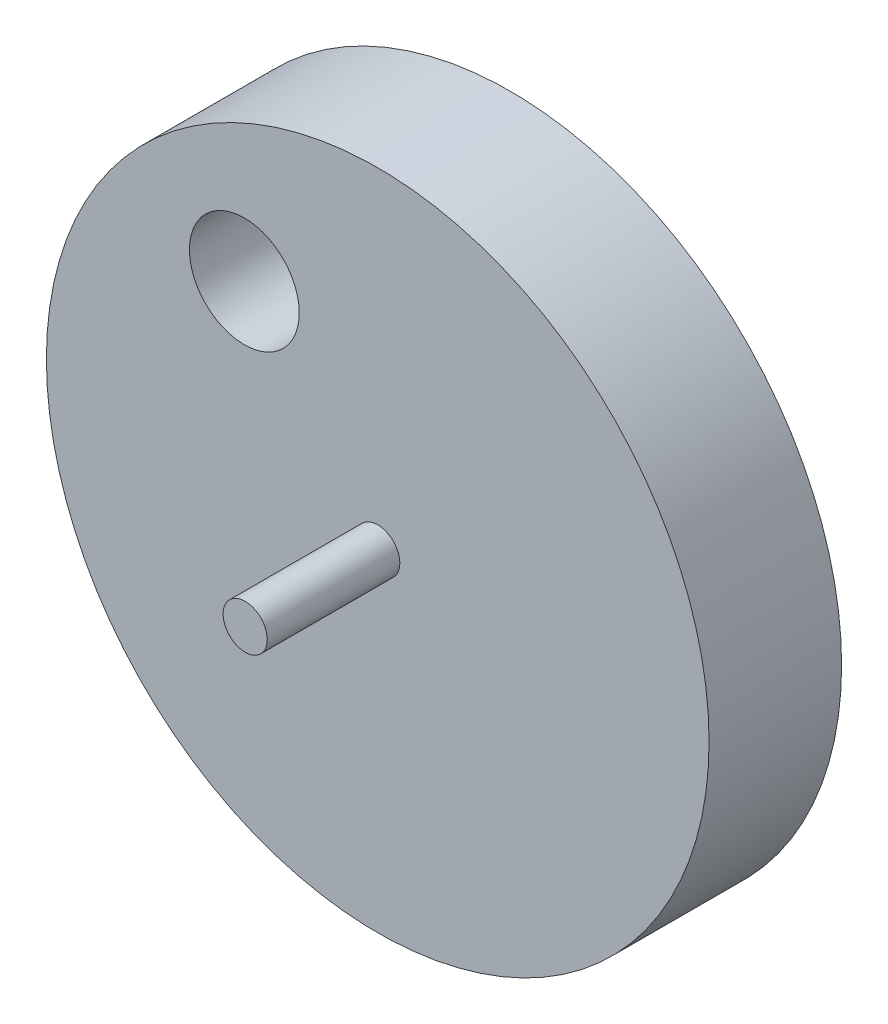
SolidWorks part; units mm, degrees
ref_plane "前视基准面" through (0, 0, 0) normal (0, 0, 1) x (1, 0, 0)
ref_plane "上视基准面" through (0, 0, 0) normal (0, 1, 0) x (1, 0, 0)
ref_plane "右视基准面" through (0, 0, 0) normal (1, 0, 0) x (0, 0, -1)
sketch "草图1" plane through (0, 0, 0) normal (0, 0, 1) x (1, 0, 0)
  circle A0 centre (0, 0) radius 75
  circle A1 centre (0, 0) radius 5
  circle A2 centre (-30.195, 37.6255) radius 12.4275
  dimension "D1" = 150
  dimension "D2" = 10
extrude "凸台-拉伸1" add sketch "草图1" along normal blind 30
sketch "草图2" plane through (0, 0, 30) normal (0, 0, 1) x (1, 0, 0)
  circle A0 centre (0, 0) radius 5
extrude "凸台-拉伸2" add sketch "草图2" along normal blind 30 and the other way blind 60
